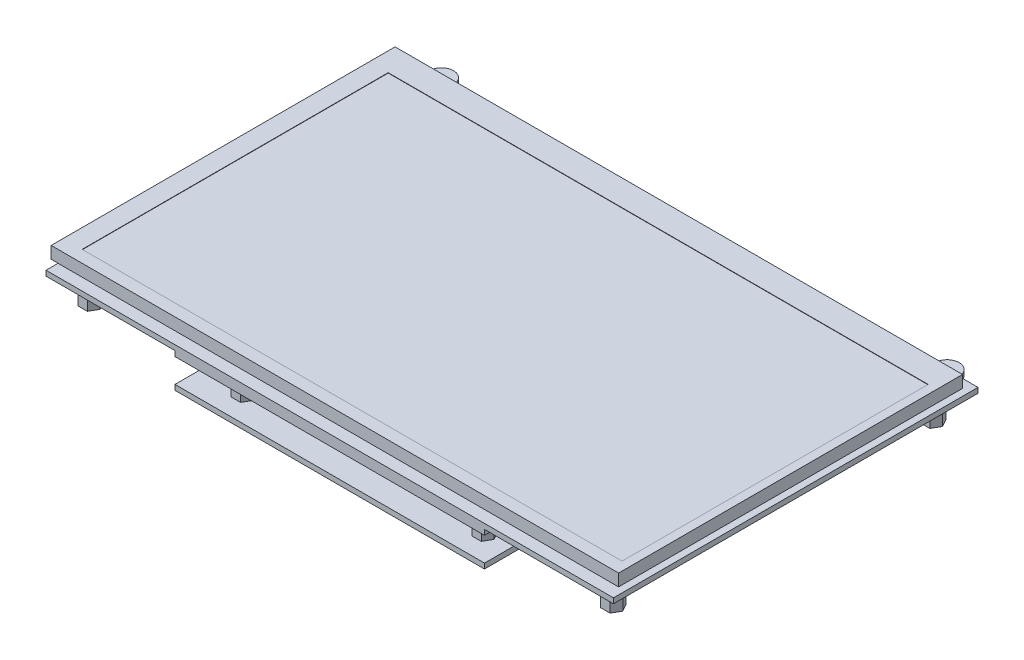
SolidWorks part; units mm, degrees
ref_plane "前视基准面" through (0, 0, 0) normal (0, 0, 1) x (1, 0, 0)
ref_plane "上视基准面" through (0, 0, 0) normal (0, 1, 0) x (1, 0, 0)
ref_plane "右视基准面" through (0, 0, 0) normal (1, 0, 0) x (0, 0, -1)
sketch "草图1" plane through (0, 0, 0) normal (0, 1, 0) x (1, 0, 0)
  line L1 (82.5, -50) -> (-82.5, -50)
  line L2 (82.5, -50) -> (82.5, 50)
  line L3 (82.5, 50) -> (-82.5, 50)
  line L4 (-82.5, -50) -> (-82.5, 50)
  line L5 (82.5, -50) -> (-82.5, 50) construction
  line L6 (82.5, 50) -> (-82.5, -50) construction
  point P0 (0, 0)
  dimension "D1" = 100
  dimension "D2" = 165
extrude "凸台-拉伸1" add sketch "草图1" along normal blind 3.5
sketch "草图2" plane through (0, 0, 0) normal (0, -1, 0) x (1, 0, 0)
  line L0 (-82.5, 50) -> (82.5, 50) construction
  line L1 (17.5, 33) -> (-17.5, 33)
  line L2 (17.5, 33) -> (17.5, 45)
  line L3 (17.5, 45) -> (-17.5, 45)
  line L4 (-17.5, 33) -> (-17.5, 45)
  line L5 (17.5, 33) -> (-17.5, 45) construction
  line L6 (17.5, 45) -> (-17.5, 33) construction
  line L7 (0, 89.4671) -> (0, -87.6416) construction
  line L12 (-82.5, -50) -> (-82.5, 50) construction
  line L13 (-72.5, -40) -> (-77.5, -40)
  line L14 (-72.5, -40) -> (-72.5, 40)
  line L15 (-72.5, 40) -> (-77.5, 40)
  line L16 (-77.5, -40) -> (-77.5, 40)
  line L17 (-72.5, -40) -> (-77.5, 40) construction
  line L18 (-72.5, 40) -> (-77.5, -40) construction
  line L19 (72.5, 40) -> (77.5, 40)
  line L20 (77.5, -40) -> (77.5, 40)
  line L21 (72.5, -40) -> (77.5, -40)
  line L22 (72.5, -40) -> (72.5, 40)
  line L23 (82.5, -50) -> (-82.5, -50) construction
  line L24 (-57.5, -33) -> (-27.5, -33)
  line L25 (-57.5, -33) -> (-57.5, -45)
  line L26 (-57.5, -45) -> (-27.5, -45)
  line L27 (-27.5, -33) -> (-27.5, -45)
  line L28 (-57.5, -33) -> (-27.5, -45) construction
  line L29 (-57.5, -45) -> (-27.5, -33) construction
  point P0 (0, 39)
  point P10 (-75, 0)
  point P15 (-42.5, -39)
  dimension "D1" = 35
  dimension "D2" = 12
  dimension "D3" = 5
  dimension "D4" = 5
  dimension "D5" = 80
  dimension "D6" = 5
  dimension "D7" = 30
  dimension "D8" = 12
  dimension "D9" = 5
  dimension "D10" = 25
extrude "凸台-拉伸2" add sketch "草图2" along normal blind 2
sketch "草图3" plane through (0, -2, 0) normal (0, -1, 0) x (1, 0, 0)
  line L0 (-82.5, -50) -> (-82.5, 50) construction
  line L1 (82.5, -54.5) -> (77, -54.5)
  line L2 (82.5, -54.5) -> (82.5, 51.5)
  line L3 (82.5, 51.5) -> (-82.5, 51.5)
  line L4 (-82.5, -54.5) -> (-82.5, 51.5)
  line L5 (82.5, -54.5) -> (-82.5, 51.5) construction
  line L6 (82.5, 51.5) -> (-82.5, -54.5) construction
  line L7 (-82.5, 50) -> (82.5, 50) construction
  line L8 (0, 72.3689) -> (0, -90.7086) construction
  line L9 (-77, -54.5) -> (-82.5, -54.5)
  line L10 (70, -54.5) -> (-70, -54.5)
  arc A0 (-77, -54.5) -> (-70, -54.5) centre (-73.5, -54.5) ccw
  arc A1 (77, -54.5) -> (70, -54.5) centre (73.5, -54.5) cw
  point P0 (0, -1.5)
  dimension "D5" = 7
  dimension "D1" = 165
  dimension "D2" = 106
  dimension "D3" = 1.5
  dimension "D4" = 9
extrude "凸台-拉伸3" add sketch "草图3" along normal blind 1.5
sketch "草图4" plane through (0, -3.5, 0) normal (0, -1, 0) x (1, 0, 0)
  line L0 (82.5, 51.5) -> (-82.5, 51.5) construction
  line L1 (45, -12.5) -> (-45, -12.5)
  line L2 (45, -12.5) -> (45, 51.5)
  line L3 (45, 51.5) -> (-45, 51.5)
  line L4 (-45, -12.5) -> (-45, 51.5)
  line L5 (45, -12.5) -> (-45, 51.5) construction
  line L6 (45, 51.5) -> (-45, -12.5) construction
  point P0 (0, 19.5)
  point P7 (0, 0)
  dimension "D1" = 90
  dimension "D2" = 64
extrude "凸台-拉伸4" add sketch "草图4" along normal blind 1.5
sketch "草图5" plane through (0, -5, 0) normal (0, -1, 0) x (1, 0, 0)
  line L0 (-33.6432, 46.5) -> (-30.9297, 46.5)
  line L1 (-30.9297, 46.5) -> (-29.5729, 44.15)
  line L2 (-29.5729, 44.15) -> (-30.9297, 41.8)
  line L3 (-30.9297, 41.8) -> (-33.6432, 41.8)
  line L4 (-33.6432, 41.8) -> (-35, 44.15)
  line L5 (-35, 44.15) -> (-33.6432, 46.5)
  line L6 (45, 51.5) -> (-45, 51.5) construction
  line L7 (-45, 51.5) -> (-45, -12.5) construction
  line L8 (-45, 19.5) -> (45, 19.5) construction
  line L9 (-45, 51.5) -> (-45, -12.5) construction
  line L10 (45, -12.5) -> (45, 51.5) construction
  line L11 (35, 44.15) -> (36.3568, 46.5)
  line L12 (36.3568, 46.5) -> (39.0703, 46.5)
  line L13 (39.0703, 46.5) -> (40.4271, 44.15)
  line L14 (40.4271, 44.15) -> (39.0703, 41.8)
  line L15 (39.0703, 41.8) -> (36.3568, 41.8)
  line L16 (36.3568, 41.8) -> (35, 44.15)
  line L17 (36.3568, -2.8) -> (35, -5.15)
  line L18 (39.0703, -2.8) -> (36.3568, -2.8)
  line L19 (40.4271, -5.15) -> (39.0703, -2.8)
  line L20 (39.0703, -7.5) -> (40.4271, -5.15)
  line L21 (36.3568, -7.5) -> (39.0703, -7.5)
  line L22 (35, -5.15) -> (36.3568, -7.5)
  line L23 (-33.6432, -2.8) -> (-35, -5.15)
  line L24 (-30.9297, -2.8) -> (-33.6432, -2.8)
  line L25 (-29.5729, -5.15) -> (-30.9297, -2.8)
  line L26 (-30.9297, -7.5) -> (-29.5729, -5.15)
  line L27 (-33.6432, -7.5) -> (-30.9297, -7.5)
  line L28 (-35, -5.15) -> (-33.6432, -7.5)
  line L29 (-35, 44.15) -> (-29.5729, 44.15) construction
  line L30 (-33.6432, 46.5) -> (-30.9297, 41.8) construction
  circle A0 centre (-32.2865, 44.15) radius 1.5
  circle A1 centre (37.7135, 44.15) radius 1.5
  circle A2 centre (37.7135, -5.15) radius 1.5
  circle A3 centre (-32.2865, -5.15) radius 1.5
  dimension "D9" = 3
  dimension "D1" = 4.7
  dimension "D2" = 4.7
  dimension "D3" = 4.7
  dimension "D4" = 120
  dimension "D5" = 120
  dimension "D6" = 5
  dimension "D7" = 10
  dimension "D8" = 2
  dimension "D10" = 2
extrude "凸台-拉伸5" add sketch "草图5" along normal blind 7
sketch "草图6" plane through (0, -12, 0) normal (0, -1, 0) x (1, 0, 0)
  line L1 (45, -12.5) -> (-45, -12.5)
  line L2 (45, -12.5) -> (45, 51.5)
  line L3 (45, 51.5) -> (-45, 51.5)
  line L4 (-45, -12.5) -> (-45, 51.5)
  line L5 (45, -12.5) -> (-45, 51.5) construction
  line L6 (45, 51.5) -> (-45, -12.5) construction
  line L7 (-42.5, 43.5) -> (-35.7, 43.5)
  line L8 (-42.5, 43.5) -> (-42.5, 27.5)
  line L9 (-42.5, 27.5) -> (-35.7, 27.5)
  line L10 (-35.7, 43.5) -> (-35.7, 27.5)
  line L11 (-42.5, 43.5) -> (-35.7, 27.5) construction
  line L12 (-42.5, 27.5) -> (-35.7, 43.5) construction
  line L13 (-42.5, 24.5) -> (-35.7, 24.5)
  line L14 (-42.5, 24.5) -> (-42.5, 14)
  line L15 (-42.5, 14) -> (-35.7, 14)
  line L16 (-35.7, 24.5) -> (-35.7, 14)
  line L17 (-42.5, 24.5) -> (-35.7, 14) construction
  line L18 (-42.5, 14) -> (-35.7, 24.5) construction
  line L19 (-42.5, 11.5) -> (-35.7, 11.5)
  line L20 (-42.5, 11.5) -> (-42.5, 1)
  line L21 (-42.5, 1) -> (-35.7, 1)
  line L22 (-35.7, 11.5) -> (-35.7, 1)
  line L23 (-42.5, 11.5) -> (-35.7, 1) construction
  line L24 (-42.5, 1) -> (-35.7, 11.5) construction
  line L25 (-42.5, -1) -> (-35.7, -1)
  line L26 (-42.5, -1) -> (-42.5, -9.5)
  line L27 (-42.5, -9.5) -> (-35.7, -9.5)
  line L28 (-35.7, -1) -> (-35.7, -9.5)
  line L29 (-42.5, -1) -> (-35.7, -9.5) construction
  line L30 (-42.5, -9.5) -> (-35.7, -1) construction
  line L31 (28.9126, 20.75) -> (33.9126, 20.75)
  line L32 (28.9126, 20.75) -> (28.9126, 18.25)
  line L33 (28.9126, 18.25) -> (33.9126, 18.25)
  line L34 (33.9126, 20.75) -> (33.9126, 18.25)
  line L35 (28.9126, 20.75) -> (33.9126, 18.25) construction
  line L36 (28.9126, 18.25) -> (33.9126, 20.75) construction
  point P0 (0, 19.5)
  point P6 (-39.1, 35.5)
  point P11 (-39.1, 19.25)
  point P16 (-39.1, 6.25)
  point P21 (-39.1, -5.25)
  point P26 (31.4126, 19.5)
  point P31 (0, 0)
  dimension "D1" = 64
  dimension "D2" = 6.8
  dimension "D3" = 6.8
  dimension "D4" = 6.8
  dimension "D5" = 6.8
  dimension "D6" = 16
  dimension "D7" = 10.5
  dimension "D8" = 10.5
  dimension "D9" = 8.5
  dimension "D10" = 2.5
  dimension "D11" = 3
  dimension "D12" = 2.5
  dimension "D13" = 2
  dimension "D14" = 3
  dimension "D15" = 5
  dimension "D16" = 2.5
extrude "凸台-拉伸6" add sketch "草图6" along normal blind 1.5
sketch "草图7" plane through (0, -3.5, 0) normal (0, -1, 0) x (1, 0, 0)
  line L0 (-77.3568, 47.35) -> (-74.6432, 47.35)
  line L1 (-74.6432, 47.35) -> (-73.2865, 45)
  line L2 (-73.2865, 45) -> (-74.6432, 42.65)
  line L3 (-74.6432, 42.65) -> (-77.3568, 42.65)
  line L4 (-77.3568, 42.65) -> (-78.7135, 45)
  line L5 (-78.7135, 45) -> (-77.3568, 47.35)
  line L6 (-78.7135, 45) -> (-73.2865, 45) construction
  line L7 (-77.3568, 47.35) -> (-74.6432, 42.65) construction
  line L8 (-82.5, 51.5) -> (-82.5, -54.5) construction
  line L9 (-45, 51.5) -> (-82.5, 51.5) construction
  line L10 (73.2865, 45) -> (74.6432, 47.35)
  line L11 (74.6432, 47.35) -> (77.3568, 47.35)
  line L12 (77.3568, 47.35) -> (78.7135, 45)
  line L13 (78.7135, 45) -> (77.3568, 42.65)
  line L14 (77.3568, 42.65) -> (74.6432, 42.65)
  line L15 (74.6432, 42.65) -> (73.2865, 45)
  line L16 (-82.5, -1.5) -> (82.5, -1.5) construction
  line L17 (82.5, -54.5) -> (82.5, 51.5) construction
  line L18 (74.6432, -45.65) -> (73.2865, -48)
  line L19 (77.3568, -45.65) -> (74.6432, -45.65)
  line L20 (78.7135, -48) -> (77.3568, -45.65)
  line L21 (77.3568, -50.35) -> (78.7135, -48)
  line L22 (74.6432, -50.35) -> (77.3568, -50.35)
  line L23 (73.2865, -48) -> (74.6432, -50.35)
  line L24 (-77.3568, -45.65) -> (-78.7135, -48)
  line L25 (-74.6432, -45.65) -> (-77.3568, -45.65)
  line L26 (-73.2865, -48) -> (-74.6432, -45.65)
  line L27 (-74.6432, -50.35) -> (-73.2865, -48)
  line L28 (-77.3568, -50.35) -> (-74.6432, -50.35)
  line L29 (-78.7135, -48) -> (-77.3568, -50.35)
  circle A0 centre (-76, 45) radius 1.5
  circle A1 centre (76, 45) radius 1.5
  circle A2 centre (76, -48) radius 1.5
  circle A3 centre (-76, -48) radius 1.5
  dimension "D6" = 3
  dimension "D1" = 4.7
  dimension "D2" = 4.7
  dimension "D3" = 4.7
  dimension "D4" = 120
  dimension "D5" = 120
  dimension "D7" = 6.5
  dimension "D8" = 6.5
  dimension "D10" = 6.5
  dimension "D9" = 2
extrude "凸台-拉伸7" add sketch "草图7" along normal blind 7
sketch "草图8" plane through (0, 3.5, 0) normal (0, 1, 0) x (1, 0, 0)
  line L0 (-82.5, -50) -> (82.5, -50) construction
  line L1 (80, -46.5) -> (-77, -46.5)
  line L2 (80, -46.5) -> (80, 42.5)
  line L3 (80, 42.5) -> (-77, 42.5)
  line L4 (-77, -46.5) -> (-77, 42.5)
  line L5 (82.5, -50) -> (82.5, 50) construction
  line L6 (82.5, 50) -> (-82.5, 50) construction
  line L7 (-82.5, 50) -> (-82.5, -50) construction
  dimension "D1" = 3.5
  dimension "D2" = 2.5
  dimension "D3" = 7.5
  dimension "D4" = 5.5
extrude "切除-拉伸1" cut sketch "草图8" against normal blind 0.1
